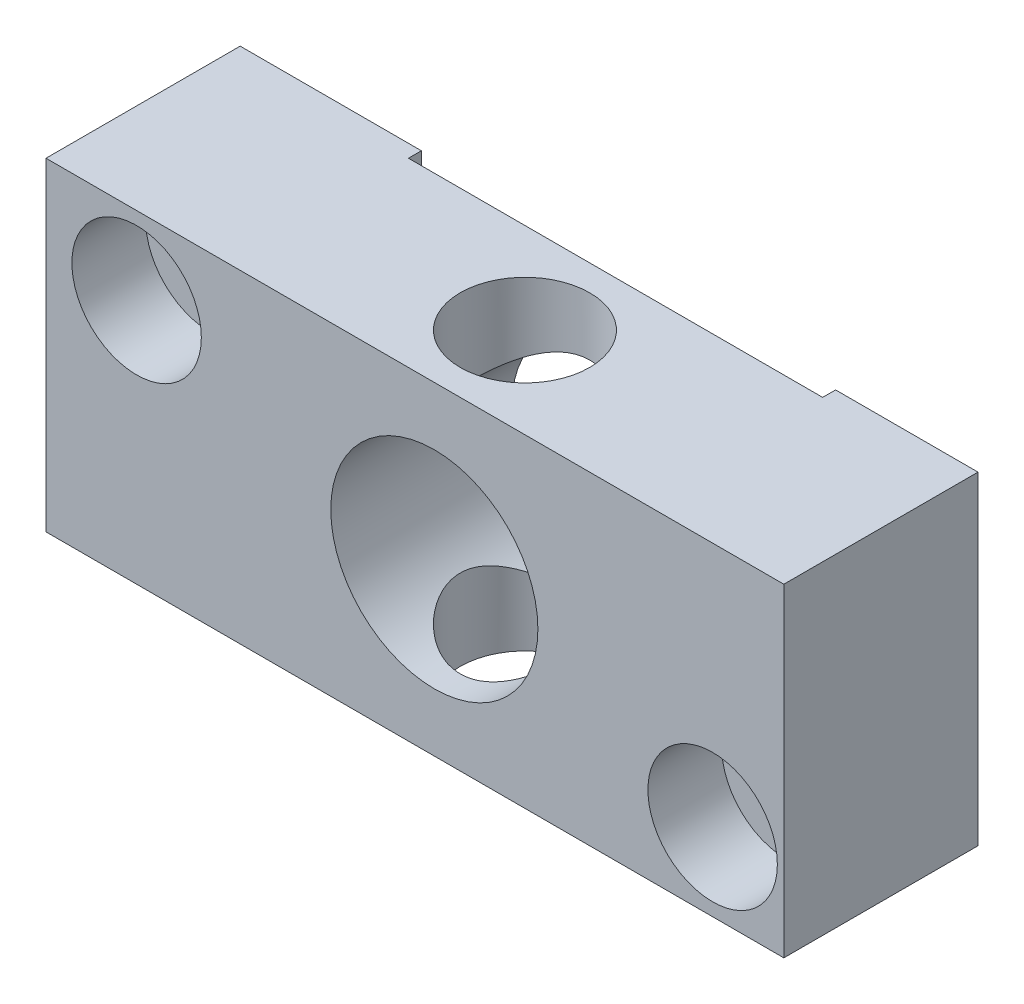
SolidWorks part; units mm, degrees
ref_plane "Front Plane" through (0, 0, 0) normal (0, 0, 1) x (1, 0, 0)
ref_plane "Top Plane" through (0, 0, 0) normal (0, 1, 0) x (1, 0, 0)
ref_plane "Right Plane" through (0, 0, 0) normal (1, 0, 0) x (0, 0, -1)
sketch "Sketch1" plane through (0, 0, 0) normal (0, 1, 0) x (1, 0, 0)
  line L0 (-14.5, 7.5) -> (-14.5, 6.5)
  line L1 (-28.5, -7.5) -> (28.5, -7.5)
  line L2 (-28.5, -7.5) -> (-28.5, 7.5)
  line L3 (-28.5, 7.5) -> (-14.5, 7.5)
  line L4 (28.5, -7.5) -> (28.5, 7.5)
  line L5 (-28.5, -7.5) -> (28.5, 7.5) construction
  line L6 (-28.5, 7.5) -> (28.5, -7.5) construction
  line L7 (-14.5, 6.5) -> (17.5, 6.5)
  line L8 (17.5, 6.5) -> (17.5, 7.5)
  line L9 (17.5, 7.5) -> (28.5, 7.5)
  circle A0 centre (1.5, -0.5) radius 5
  point P0 (0, 0)
  dimension "D6" = 30
  dimension "D7" = 7
  dimension "D1" = 15
  dimension "D2" = 57
  dimension "D3" = 14
  dimension "D4" = 11
  dimension "D5" = 1
extrude "Boss-Extrude2" add sketch "Sketch1" along normal blind 25
sketch "Sketch3" plane through (0, 0, 7.5) normal (0, 0, 1) x (1, 0, 0)
  line L0 (-28.5, 25) -> (-28.5, 0) construction
  line L1 (-28.5, 0) -> (28.5, 0) construction
  line L2 (28.5, 25) -> (28.5, 0) construction
  circle A0 centre (-21.5, 19) radius 2.75
  circle A1 centre (1.5, 12.5) radius 8
  circle A2 centre (23, 6) radius 2.75
  dimension "D1" = 5.5
  dimension "D2" = 16
  dimension "D3" = 5.5
  dimension "D4" = 7
  dimension "D5" = 19
  dimension "D6" = 12.5
  dimension "D7" = 30
  dimension "D8" = 6
  dimension "D9" = 5.5
extrude "Cut-Extrude1" cut sketch "Sketch3" against normal through all
sketch "Sketch4" plane through (0, 0, 7.5) normal (0, 0, 1) x (1, 0, 0)
  circle A0 centre (-21.5, 19) radius 5
  circle A1 centre (23, 6) radius 5
extrude "Cut-Extrude2" cut sketch "Sketch4" against normal blind 5.7
